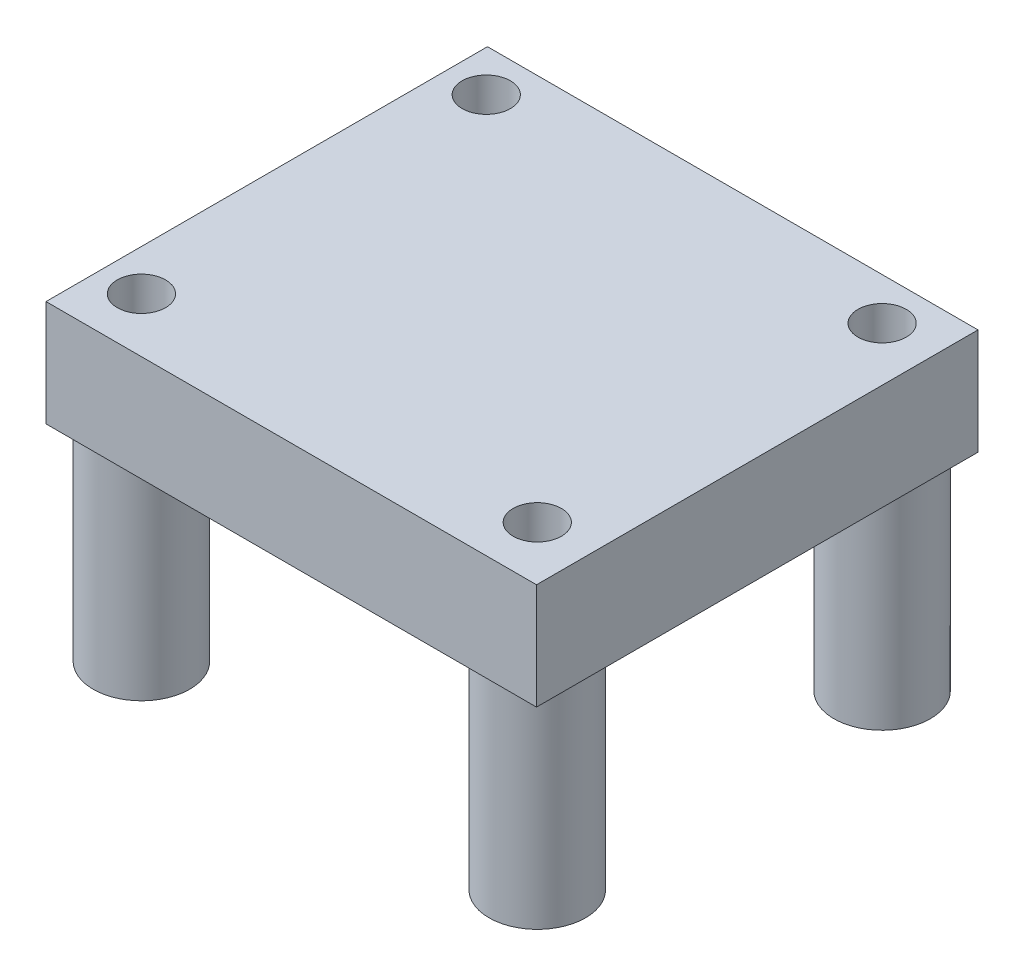
SolidWorks part; units mm, degrees
ref_plane "Front Plane" through (0, 0, 0) normal (0, 0, 1) x (1, 0, 0)
ref_plane "Top Plane" through (0, 0, 0) normal (0, 1, 0) x (1, 0, 0)
ref_plane "Right Plane" through (0, 0, 0) normal (1, 0, 0) x (0, 0, -1)
sketch "Sketch1" plane through (0, 0, 0) normal (0, 1, 0) x (1, 0, 0)
  line L0 (-34.0407, 1.6731) -> (-34.0407, -21.1869)
  line L1 (-34.0407, -21.1869) -> (-8.6407, -21.1869)
  line L2 (-8.6407, -21.1869) -> (-8.6407, 1.6731)
  line L3 (-8.6407, 1.6731) -> (-34.0407, 1.6731)
  dimension "D1" = 22.86
  dimension "D2" = 25.4
extrude "Boss-Extrude1" add sketch "Sketch1" along normal blind 5.4864
sketch "Sketch2" plane through (0, 0, 0) normal (0, -1, 0) x (1, 0, 0)
  circle A0 centre (-31.9185, 18.3679) radius 2.5
  circle A1 centre (-11.4207, 18.3679) radius 1.25
  circle A2 centre (-31.9185, 0.5117) radius 1.25
  circle A3 centre (-11.4207, 0.5117) radius 1.25
  circle A4 centre (-31.9185, 18.3679) radius 1.25
  circle A5 centre (-31.9185, 0.5117) radius 2.5
  circle A6 centre (-11.4207, 0.5117) radius 2.5
  circle A7 centre (-11.4207, 18.3679) radius 2.5
  dimension "D1" = 5
  dimension "D2" = 2.5
  dimension "D3" = 2.5
  dimension "D4" = 5
  dimension "D5" = 2.5
  dimension "D6" = 5
  dimension "D7" = 2.5
  dimension "D8" = 5
  dimension "D9" = 17.8562
  dimension "D11" = 20.4978
extrude "Boss-Extrude2" add sketch "Sketch2" along normal blind 11
sketch "Sketch5" plane through (0, 5.4864, 0) normal (0, 1, 0) x (1, 0, 0)
  circle A0 centre (-31.9185, -0.5117) radius 1.25
  circle A1 centre (-11.4207, -0.5117) radius 1.25
  circle A2 centre (-11.4207, -18.3679) radius 1.25
  circle A3 centre (-31.9185, -18.3679) radius 1.25
  dimension "D1" = 2.5
  dimension "D2" = 2.5
  dimension "D3" = 2.5
  dimension "D4" = 2.5
extrude "Cut-Extrude1" cut sketch "Sketch5" against normal through all both and the other way through all
